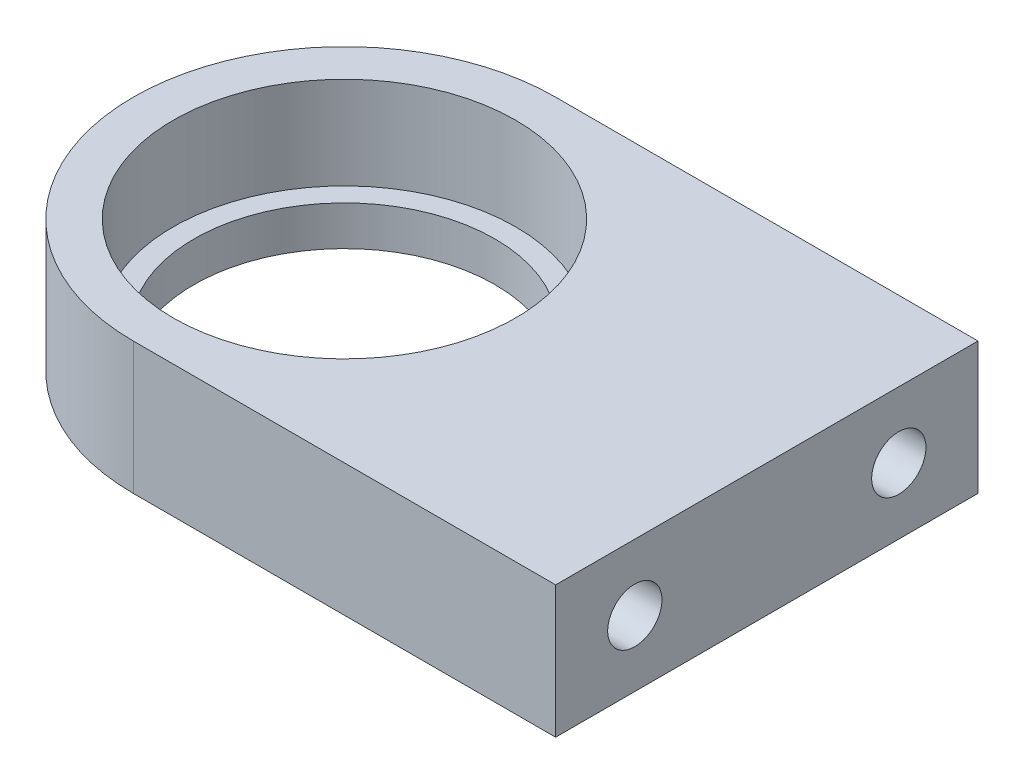
SolidWorks part; units mm, degrees
material "6061-T6 (SS)"
ref_plane "Front Plane" through (0, 0, 0) normal (0, 0, 1) x (1, 0, 0)
ref_plane "Top Plane" through (0, 0, 0) normal (0, 1, 0) x (1, 0, 0)
ref_plane "Right Plane" through (0, 0, 0) normal (1, 0, 0) x (0, 0, -1)
sketch "Sketch1" plane through (0, 0, 0) normal (0, 1, 0) x (1, 0, 0)
  line L0 (-25.4, 25.4) -> (-25.4, -25.4)
  line L1 (-25.4, -25.4) -> (50.8, -25.4)
  line L2 (50.8, -25.4) -> (50.8, 25.4)
  line L3 (50.8, 25.4) -> (-25.4, 25.4)
  line L4 (-20.955, 0) -> (20.955, 0) construction
  line L5 (0, -20.955) -> (0, 20.955) construction
  dimension "D1" = 25.4
  dimension "D2" = 50.8
  dimension "D3" = 76.2
  dimension "D4" = 25.4
extrude "Boss-Extrude1" add sketch "Sketch1" along normal mid plane 15.875
sketch "Sketch2" plane through (0, 7.9375, 0) normal (0, 1, 0) x (1, 0, 0)
  circle A0 centre (0, 0) radius 20.5994
  dimension "D1" = 41.1988
extrude "Cut-Extrude1" cut sketch "Sketch2" against normal blind 11.1125
sketch "Sketch3" plane through (0, -3.175, 0) normal (0, 1, 0) x (1, 0, 0)
  circle A0 centre (0, 0) radius 18.0975
  dimension "D1" = 36.195
extrude "Cut-Extrude2" cut sketch "Sketch3" against normal blind 12.7
sketch "Sketch7" plane through (50.8, 0, 0) normal (1, 0, 0) x (0, 0, -1)
  line L1 (-25.4, 7.9375) -> (-25.4, -7.9375) construction
  line L3 (15.875, 0) -> (-15.875, 0) construction
  circle A0 centre (-15.875, 0) radius 3.2639
  circle A1 centre (15.875, 0) radius 3.2639
  point P0 (0, 0)
  dimension "D3" = 6.5278
  dimension "D1" = 9.525
extrude "Cut-Extrude6" cut sketch "Sketch7" against normal blind 19.05
sketch "Sketch8" plane through (0, 7.9375, 0) normal (0, 1, 0) x (1, 0, 0)
  line L3 (-25.4, -25.4) -> (50.8, -25.4) construction
  line L4 (0, -8.7312) -> (0, 8.7312) construction
  line L5 (50.8, 25.4) -> (-25.4, 25.4) construction
  line L6 (0, -25.4) -> (0, -38.1)
  line L7 (0, -38.1) -> (-50.8, -38.1)
  line L8 (-50.8, -38.1) -> (-50.8, 38.1)
  line L9 (-50.8, 38.1) -> (0, 38.1)
  line L10 (0, 38.1) -> (0, 25.4)
  arc A0 (0, -25.4) -> (0, 25.4) centre (0, 0) cw
  circle A2 centre (0, 0) radius 20.5994 construction
  dimension "D1" = 12.7
  dimension "D2" = 12.7
  dimension "D3" = 50.8
extrude "Cut-Extrude7" cut sketch "Sketch8" against normal through all
